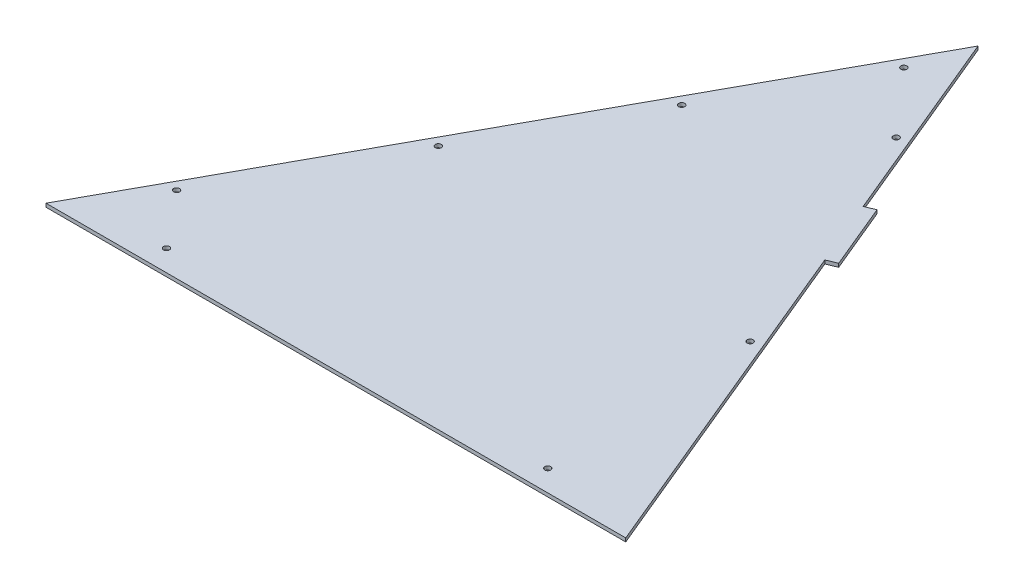
SolidWorks part; units mm, degrees
material "PE High Density"
ref_plane "Front Plane" through (0, 0, 0) normal (0, 0, 1) x (1, 0, 0)
ref_plane "Top Plane" through (0, 0, 0) normal (0, 1, 0) x (1, 0, 0)
ref_plane "Right Plane" through (0, 0, 0) normal (1, 0, 0) x (0, 0, -1)
sketch "Sketch4" plane through (0, 0, 0) normal (0, 1, 0) x (1, 0, 0)
  line L0 (-356.1703, 0) -> (682.6897, 0)
  line L1 (682.6897, 0) -> (234.9792, 1078.9716)
  line L2 (234.9792, 1078.9716) -> (-356.1703, 0)
  line L3 (381.0003, 727.0642) -> (398.5957, 734.3653)
  line L4 (398.5957, 734.3653) -> (447.2694, 617.0628)
  line L5 (447.2694, 617.0628) -> (429.674, 609.7617)
  line L6 (429.674, 609.7617) -> (381.0003, 727.0642)
  line L9 (664.3232, 0) -> (-326.0136, 0) construction
  circle A2 centre (303.6675, 863.7291) radius 5.3578
  circle A3 centre (489.2933, 416.3753) radius 5.3578
  circle A5 centre (61.0945, 721.9489) radius 5.3578
  circle A6 centre (-93.2898, 440.1652) radius 5.3578
  circle A7 centre (-259.301, 137.16) radius 5.3578
  circle A9 centre (504.8897, 38.1) radius 5.3578
  circle A10 centre (-178.3703, 38.1) radius 5.3578
  circle A11 centre (201.9739, 979.0832) radius 5.3578
  dimension "D4" = 10.7156
  dimension "D5" = 19.05
  dimension "D6" = 10.7156
  dimension "D10" = 10.7156
  dimension "D12" = 10.7156
  dimension "D13" = 127
  dimension "D14" = 10.7156
  dimension "D15" = 10.7156
  dimension "D16" = 10.7156
  dimension "D1" = 1038.86
  dimension "D2" = 1168.1714
  dimension "D3" = 1230.2998
  dimension "D7" = 19.05
  dimension "D8" = 19.05
  dimension "D9" = 19.05
  dimension "D11" = 38.1
  dimension "D17" = 137.16
  dimension "D18" = 381
  dimension "D20" = 38.1
  dimension "D21" = 177.8
  dimension "D22" = 19.05
  dimension "D23" = 19.05
  dimension "D24" = 177.8
  dimension "D25" = 19.05
extrude "Boss-Extrude2" add sketch "Sketch4" along normal blind 6.35
sketch "Sketch5" plane through (0, 6.35, 0) normal (0, 1, 0) x (1, 0, 0)
  line L0 (-239.2238, 110.3702) -> (-227.0193, 132.6459) construction
  line L1 (-250.3617, 116.4724) -> (-238.1571, 138.7482)
  line L2 (-228.0859, 104.2679) -> (-215.8814, 126.5437)
  line L3 (-191.0703, 68.58) -> (-165.6703, 68.58) construction
  line L4 (-191.0703, 81.28) -> (-165.6703, 81.28)
  line L5 (-191.0703, 55.88) -> (-165.6703, 55.88)
  line L6 (-72.3558, 414.9391) -> (-60.1513, 437.2149) construction
  line L7 (-83.4937, 421.0413) -> (-71.2892, 443.3171)
  line L8 (-61.2179, 408.8368) -> (-49.0134, 431.1126)
  line L9 (222.745, 953.5599) -> (234.9496, 975.8357) construction
  line L10 (211.6072, 959.6622) -> (223.8117, 981.9379)
  line L11 (233.8829, 947.4576) -> (246.0874, 969.7334)
  line L12 (81.2069, 695.2231) -> (93.4668, 717.6001) construction
  line L13 (70.069, 701.3254) -> (82.3289, 723.7023)
  line L14 (92.3448, 689.1209) -> (104.6047, 711.4978)
  line L15 (270.6329, 863.8128) -> (280.3677, 840.3524) construction
  line L18 (456.0343, 416.9998) -> (465.7691, 393.5393) construction
  line L19 (467.7646, 421.8672) -> (477.4993, 398.4067)
  line L20 (444.3041, 412.1325) -> (454.0388, 388.672)
  line L21 (492.9613, 68.58) -> (518.3613, 68.58) construction
  line L22 (492.9613, 81.28) -> (518.3613, 81.28)
  line L23 (492.9613, 55.88) -> (518.3613, 55.88)
  line L24 (234.9792, 1078.9716) -> (-356.1703, 0) construction
  line L25 (-356.1703, 0) -> (682.6897, 0) construction
  line L26 (282.3632, 868.6802) -> (292.0979, 845.2197)
  line L27 (258.9027, 858.9455) -> (268.6374, 835.485)
  line L28 (682.6897, 0) -> (429.674, 609.7617) construction
  line L29 (381.0003, 727.0642) -> (234.9792, 1078.9716) construction
  arc A0 (-250.3617, 116.4724) -> (-228.0859, 104.2679) centre (-239.2238, 110.3702) ccw
  arc A1 (-215.8814, 126.5437) -> (-238.1571, 138.7482) centre (-227.0193, 132.6459) ccw
  arc A2 (-191.0703, 81.28) -> (-191.0703, 55.88) centre (-191.0703, 68.58) ccw
  arc A3 (-165.6703, 55.88) -> (-165.6703, 81.28) centre (-165.6703, 68.58) ccw
  arc A4 (-83.4937, 421.0413) -> (-61.2179, 408.8368) centre (-72.3558, 414.9391) ccw
  arc A5 (-49.0134, 431.1126) -> (-71.2892, 443.3171) centre (-60.1513, 437.2149) ccw
  arc A6 (211.6072, 959.6622) -> (233.8829, 947.4576) centre (222.745, 953.5599) ccw
  arc A7 (246.0874, 969.7334) -> (223.8117, 981.9379) centre (234.9496, 975.8357) ccw
  arc A8 (70.069, 701.3254) -> (92.3448, 689.1209) centre (81.2069, 695.2231) ccw
  arc A9 (104.6047, 711.4978) -> (82.3289, 723.7023) centre (93.4668, 717.6001) ccw
  arc A12 (467.7646, 421.8672) -> (444.3041, 412.1325) centre (456.0343, 416.9998) ccw
  arc A13 (454.0388, 388.672) -> (477.4993, 398.4067) centre (465.7691, 393.5393) ccw
  arc A14 (492.9613, 81.28) -> (492.9613, 55.88) centre (492.9613, 68.58) ccw
  arc A15 (518.3613, 55.88) -> (518.3613, 81.28) centre (518.3613, 68.58) ccw
  circle A16 centre (-178.3703, 38.1) radius 5.3578 construction
  circle A17 centre (-259.301, 137.16) radius 5.3578 construction
  circle A18 centre (-93.2898, 440.1652) radius 5.3578 construction
  arc A19 (282.3632, 868.6802) -> (258.9027, 858.9455) centre (270.6329, 863.8128) ccw
  circle A20 centre (61.0945, 721.9489) radius 5.3578 construction
  arc A22 (268.6374, 835.485) -> (292.0979, 845.2197) centre (280.3677, 840.3524) ccw
  circle A23 centre (489.2933, 416.3753) radius 5.3578 construction
  circle A24 centre (504.8897, 38.1) radius 5.3578 construction
  circle A25 centre (201.9739, 979.0832) radius 5.3578 construction
  circle A26 centre (303.6675, 863.7291) radius 5.3578 construction
  point P2 (-233.1215, 121.5081)
  point P7 (-178.3703, 68.58)
  point P14 (-66.2536, 426.077)
  point P21 (228.8473, 964.6978)
  point P28 (87.3369, 706.4116)
  point P35 (275.5003, 852.0826)
  point P42 (460.9017, 405.2696)
  point P49 (505.6613, 68.58)
  dimension "D9" = 17.78
  dimension "D10" = 17.78
  dimension "D6" = 17.78
  dimension "D1" = 25.4
  dimension "D2" = 25.4
  dimension "D3" = 17.78
  dimension "D4" = 17.78
  dimension "D5" = 17.78
  dimension "D7" = 17.78
  dimension "D8" = 17.78
  dimension "D11" = 121.5081
  dimension "D12" = 426.077
  dimension "D13" = 706.4116
  dimension "D14" = 114.2738
  dimension "D15" = 405.2696
